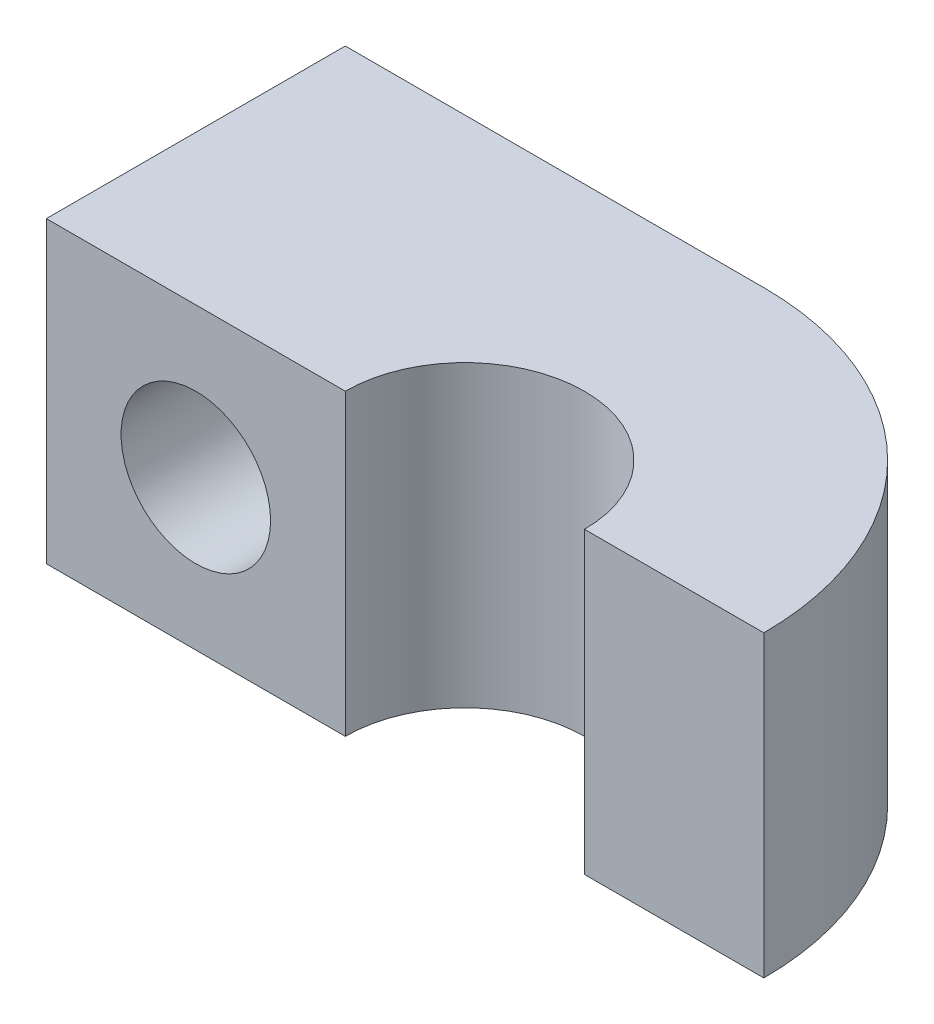
SolidWorks part; units mm, degrees
ref_plane "Спереди" through (0, 0, 0) normal (0, 0, 1) x (1, 0, 0)
ref_plane "Сверху" through (0, 0, 0) normal (0, 1, 0) x (1, 0, 0)
ref_plane "Справа" through (0, 0, 0) normal (1, 0, 0) x (0, 0, -1)
other "Configuration Table"
sketch "Эскиз1" plane through (0, 0, 0) normal (0, 1, 0) x (1, 0, 0)
  line L1 (2, 0) -> (5, 0)
  line L2 (-2, 0) -> (-7, 0)
  line L3 (-7, 0) -> (-7, 5)
  line L4 (-7, 5) -> (0, 5)
  arc A0 (2, 0) -> (-2, 0) centre (0, 0) ccw
  arc A1 (5, 0) -> (0, 5) centre (0, 0) ccw
  point P10 (-7, 4.8819)
  dimension "D1" = 2
  dimension "D2" = 3
  dimension "D3" = 5
  dimension "D4" = 5
extrude "Бобышка-Вытянуть1" add sketch "Эскиз1" along normal blind 5
sketch "Эскиз2" plane through (0, 0, 0) normal (0, 0, 1) x (1, 0, 0)
  line L0 (-4.5, 5) -> (-4.5, 0) construction
  line L1 (-7, 5) -> (-2, 5) construction
  line L2 (-7, 0) -> (-2, 0) construction
  line L3 (-7, 2.5) -> (-2, 2.5) construction
  line L4 (-7, 5) -> (-7, 0) construction
  line L5 (-2, 5) -> (-2, 0) construction
  circle A0 centre (-4.5, 2.5) radius 1.25
  dimension "D1" = 2.5
extrude "Вырез-Вытянуть1" cut sketch "Эскиз2" against normal blind 5
